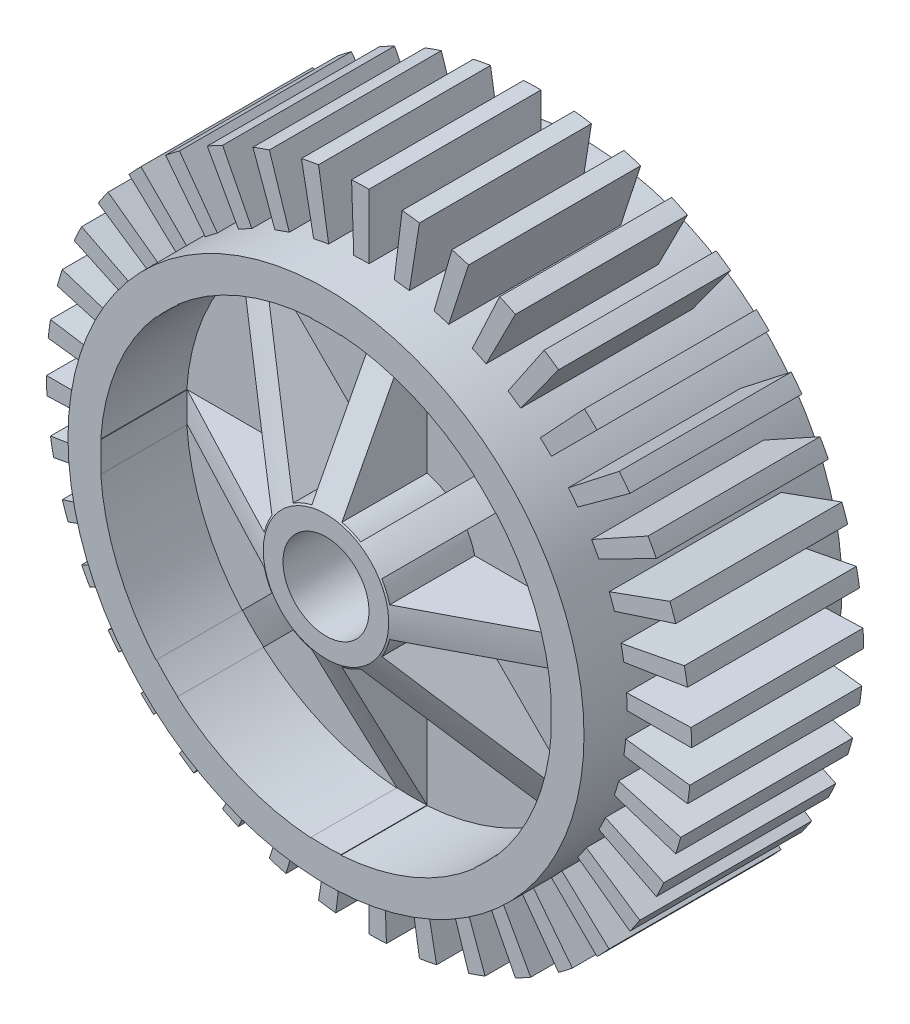
SolidWorks part; units mm, degrees
material "ABS"
ref_plane "Front Plane" through (0, 0, 0) normal (0, 0, 1) x (1, 0, 0)
ref_plane "Top Plane" through (0, 0, 0) normal (0, 1, 0) x (1, 0, 0)
ref_plane "Right Plane" through (0, 0, 0) normal (1, 0, 0) x (0, 0, -1)
sketch "Sketch1" plane through (0, 0, 0) normal (0, 0, 1) x (1, 0, 0)
  circle A0 centre (0, 0) radius 10
  circle A1 centre (0, 0) radius 75
  dimension "D1" = 20
  dimension "D2" = 150
extrude "Boss-Extrude1" add sketch "Sketch1" along normal blind 30
sketch "Sketch2" plane through (0, 0, 0) normal (0, 0, -1) x (-1, 0, 0)
  circle A0 centre (0, 0) radius 60
  circle M2 centre (0, 0) radius 75
  dimension "D1" = 120
extrude "Cut-Extrude1" cut sketch "Sketch2" against normal blind 10 contours A0 M2
sketch "Sketch3" plane through (0, 0, 0) normal (0, 0, -1) x (-1, 0, 0)
  line L0 (0, 52.5) -> (0, 15)
  line L1 (-52.5, 0) -> (-15, 0)
  line L2 (-37.1231, 37.1231) -> (-10.6066, 10.6066)
  line L3 (-37.1231, -37.1231) -> (-10.6066, -10.6066)
  line L4 (10.6066, 10.6066) -> (37.1231, 37.1231)
  line L5 (0, -15) -> (0, -52.5)
  line L6 (10.6066, -10.6066) -> (37.1231, -37.1231)
  line L7 (15, 0) -> (52.5, 0)
  line L8 (-52.3832, -3.5) -> (52.3832, -3.5)
  line L9 (-52.3832, 3.5) -> (52.3832, 3.5)
  line L10 (-3.5, 52.3832) -> (-3.5, -52.3832)
  line L11 (3.5, 52.3832) -> (3.5, -52.3832)
  line L12 (-34.5656, 39.5154) -> (39.5154, -34.5656)
  line L13 (-39.5154, 34.5656) -> (34.5656, -39.5154)
  line L14 (-34.5656, -39.5154) -> (39.5154, 34.5656)
  line L15 (-39.5154, -34.5656) -> (34.5656, 39.5154)
  circle A0 centre (0, 0) radius 52.5
  circle A1 centre (0, 0) radius 15
  dimension "D1" = 30
  dimension "D2" = 105
  dimension "D3" = 45
  dimension "D4" = 45
  dimension "D5" = 7
  dimension "D6" = 3.5
  dimension "D7" = 7
  dimension "D8" = 3.5
  dimension "D9" = 7
  dimension "D10" = 3.5
  dimension "D11" = 7
  dimension "D12" = 3.5
extrude "Cut-Extrude4" cut sketch "Sketch3" against normal blind 20 and the other way through all contours A1 L13 A0 L9 | A1 L10 A0 L12 | A1 L15 A0 L11 | A1 L9 A0 L14 | A1 L12 A0 L8 | A1 L11 A0 L13 | A1 L14 A0 L10 | A1 L8 A0 L15
sketch "Sketch6" plane through (0, 0, 0) normal (1, 0, 0) x (0, 0, -1)
  line L0 (0, -14.586) -> (-20, -52.3832)
  line L1 (-20, -52.3832) -> (0, -52.3832)
  line L2 (0, -52.3832) -> (0, -14.586)
  line L3 (0, 0) -> (-50000, 0) construction
revolve "Cut-Revolve2" cut sketch "Sketch6" angle 360 about L3
mirror "Mirror1" about plane through (0, 0, 30) normal (0, 0, 1) of bodies 106
sketch "Sketch7" plane through (0, 0, 50) normal (0, 0, 1) x (1, 0, 0)
  line L0 (0, 60) -> (0, 75)
  line L2 (5.8681, 59.7124) -> (7.7149, 74.6022)
  circle A2 centre (0, 0) radius 75 construction
  arc A3 (0, 75) -> (7.7149, 74.6022) centre (0, 0) cw
  circle A4 centre (0, 0) radius 60 construction
  circle A5 centre (0, 0) radius 60 construction
  arc A6 (0, 60) -> (5.8681, 59.7124) centre (0, 0) cw
  dimension "D1" = 7.07
  dimension "D2" = 5.8681
extrude "Cut-Extrude5" cut sketch "Sketch7" against normal up to next
pattern_circular "CirPattern1" count 40 over 360 about axis through (0, 0, 0) along (0, 0, 1) of "Cut-Extrude5"
